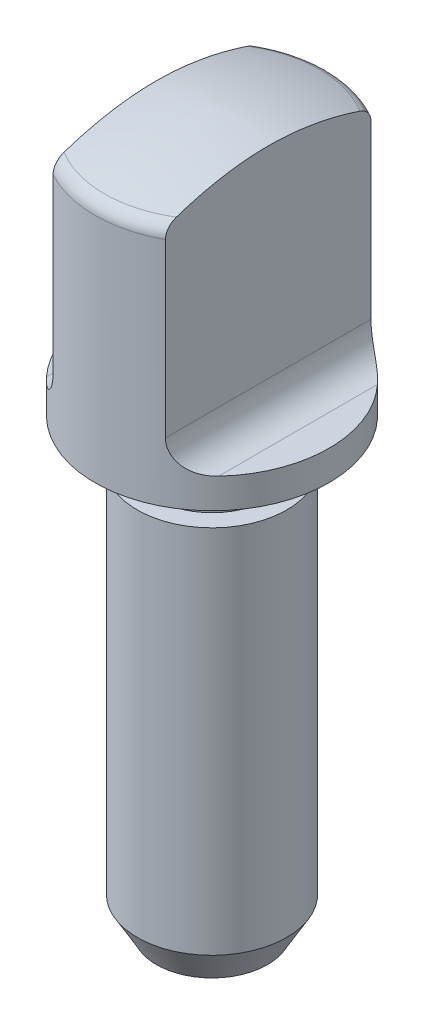
SolidWorks part; units mm, degrees
ref_plane "Front Plane" through (0, 0, 0) normal (0, 0, 1) x (1, 0, 0)
ref_plane "Top Plane" through (0, 0, 0) normal (0, 1, 0) x (1, 0, 0)
ref_plane "Right Plane" through (0, 0, 0) normal (1, 0, 0) x (0, 0, -1)
sketch "Sketch1" plane through (0, 0, 0) normal (0, 0, 1) x (1, 0, 0)
  line L0 (0, 0) -> (0, 38.1) construction
  line L2 (6.223, 36.649) -> (6.223, 23.8125)
  line L4 (3.9688, 21.4312) -> (3.9688, 0)
  line L5 (0, 0) -> (3.9688, 0)
  line L6 (0, 0) -> (0, 38.1)
  line L7 (2.9845, 23.8125) -> (2.9845, 21.4312)
  line L8 (2.9845, 23.8125) -> (6.223, 23.8125)
  line L9 (2.9845, 21.4312) -> (3.9688, 21.4312)
  arc A1 (0, 38.1) -> (6.223, 36.649) centre (-0.9863, 19.8001) cw
  point P10 (5.8989, 21.4312)
  dimension "D5" = 12.8365
  dimension "D6" = 18.3265
  dimension "D1" = 6.223
  dimension "D2" = 38.1
  dimension "D3" = 3.9688
  dimension "D4" = 23.8125
  dimension "D7" = 2.9845
  dimension "D8" = 2.3813
revolve "Revolve1" add sketch "Sketch1" angle 360 about L0
sketch "Sketch2" plane through (0, 0, 0) normal (0, 0, 1) x (1, 0, 0)
  line L0 (-6.223, 25.4) -> (-4.572, 25.4)
  line L1 (-2.9845, 23.8125) -> (2.9845, 23.8125) construction
  line L2 (-2.9845, 26.9875) -> (-2.9845, 38.1)
  line L4 (0, 38.1) -> (0, 23.8125) construction
  line L6 (6.223, 38.1) -> (6.223, 25.4)
  line L7 (-2.9845, 38.1) -> (-6.223, 38.1)
  line L8 (-6.223, 38.1) -> (-6.223, 25.4)
  line L9 (2.9845, 38.1) -> (6.223, 38.1)
  line L10 (2.9845, 26.9875) -> (2.9845, 38.1)
  line L11 (6.223, 25.4) -> (4.572, 25.4)
  line L12 (-6.223, 36.649) -> (-6.223, 23.8125) construction
  arc A0 (-4.572, 25.4) -> (-2.9845, 26.9875) centre (-4.572, 26.9875) ccw
  arc A1 (4.572, 25.4) -> (2.9845, 26.9875) centre (4.572, 26.9875) cw
  point P2 (0, 21.336)
  dimension "D1" = 1.5875
  dimension "D2" = 12.7
  dimension "D3" = 2.9845
extrude "Cut-Extrude1" cut sketch "Sketch2" against normal through all both and the other way through all contours L7 L8 L0 A0 L2 | A1 L10 L9 L6 L11
chamfer "Chamfer1" distance 1.016 angle 60 1 edges at (0, 0, -3.9688)
fillet "Fillet1" radius 0.7937 2 edges at (0, 36.649, -6.223) (0, 36.649, 6.223)
